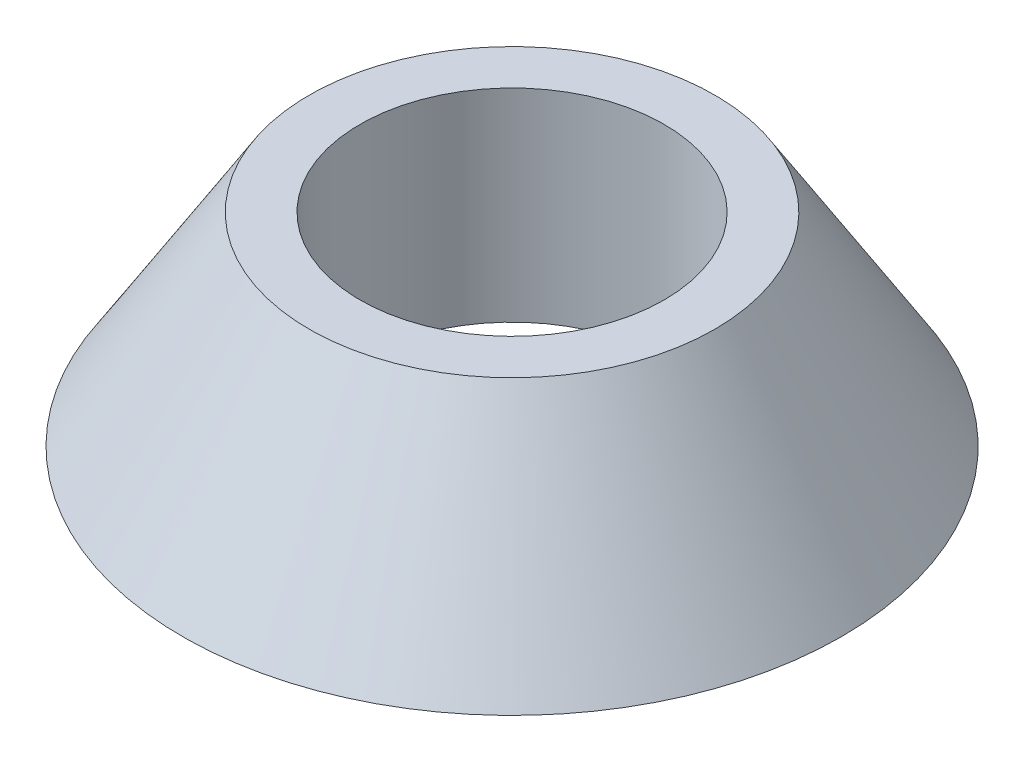
SolidWorks part; units mm, degrees
ref_plane "Płaszczyzna XY" through (0, 0, 0) normal (0, 0, 1) x (1, 0, 0)
ref_plane "Płaszczyzna XZ" through (0, 0, 0) normal (0, 1, 0) x (1, 0, 0)
ref_plane "Płaszczyzna YZ" through (0, 0, 0) normal (1, 0, 0) x (0, 0, -1)
sketch "Szkic1" plane through (0, 0, 0) normal (0, 0, 1) x (1, 0, 0)
  line L0 (0, 0) -> (0, 5.4167) construction
  line L1 (3, 0) -> (3, 4)
  line L3 (6.5, 0) -> (3, 0)
  line L4 (3, 4) -> (4, 4)
  line L5 (4, 4) -> (6.5, 0)
  dimension "D1" = 4
  dimension "D2" = 3
  dimension "D3" = 6.5
  dimension "D4" = 1
revolve "Obrót1" add sketch "Szkic1" angle 360 about L0
